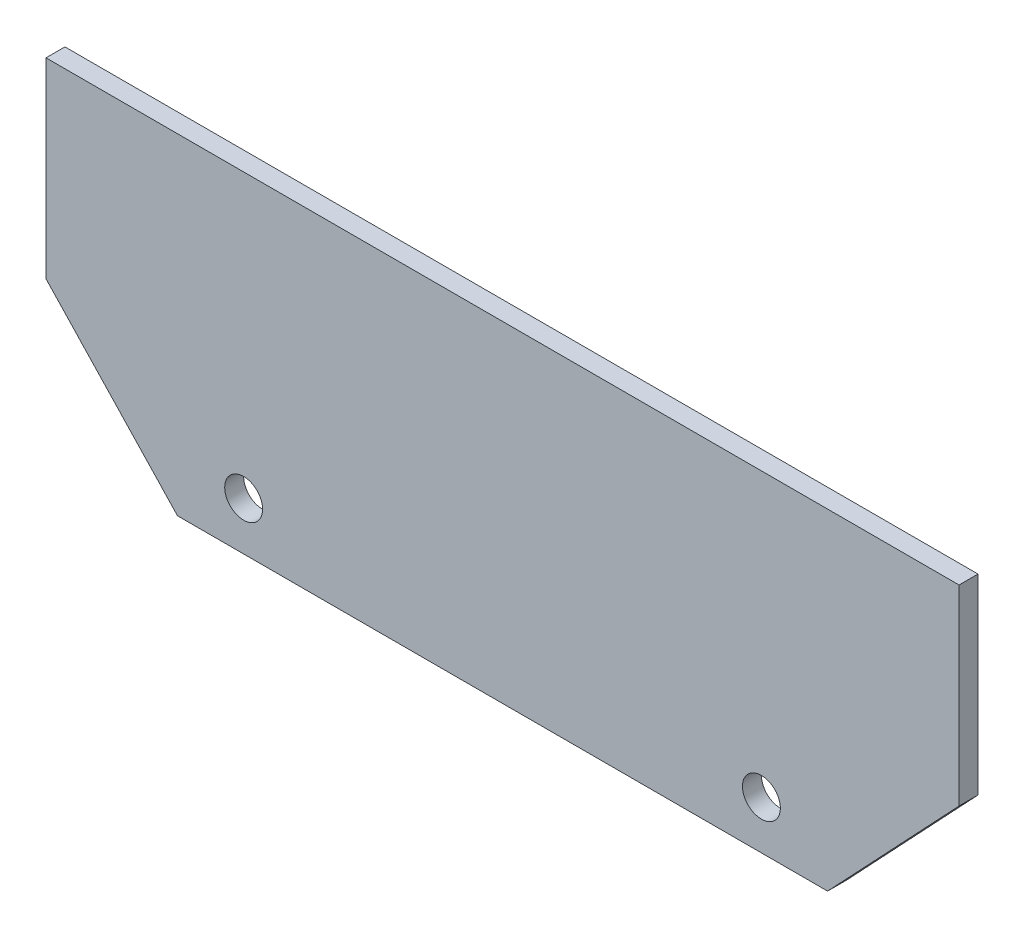
SolidWorks part; units mm, degrees
ref_plane "Front Plane" through (0, 0, 0) normal (0, 0, 1) x (1, 0, 0)
ref_plane "Top Plane" through (0, 0, 0) normal (0, 1, 0) x (1, 0, 0)
ref_plane "Right Plane" through (0, 0, 0) normal (1, 0, 0) x (0, 0, -1)
sketch "Sketch2" plane through (0, 0, 0) normal (0, 0, 1) x (1, 0, 0)
  line L0 (10.41, 0) -> (61.89, 0)
  line L2 (0, 11.0441) -> (0, 26.2)
  line L3 (0, 26.2) -> (72.3, 26.2)
  line L4 (72.3, 11.0441) -> (72.3, 26.2)
  line L5 (10.41, 0) -> (0, 11.0441)
  line L6 (61.89, 0) -> (72.3, 11.0441)
  point P7 (36.15, 26.2)
  point P8 (36.15, 0)
  dimension "D2" = 72.3
  dimension "D3" = 51.48
extrude "Boss-Extrude1" add sketch "Sketch2" along normal blind 1.5
sketch "Sketch3" plane through (0, 0, 0) normal (0, 0, -1) x (-1, 0, 0)
  line L1 (-72.3, 26.2) -> (0, 26.2) construction
  circle A0 centre (-56.65, 3.8158) radius 1.5
  circle A1 centre (-15.65, 3.8158) radius 1.5
  point P9 (-36.15, 26.2)
  dimension "D1" = 3
  dimension "D2" = 41
extrude "Cut-Extrude1" cut sketch "Sketch3" against normal through all
